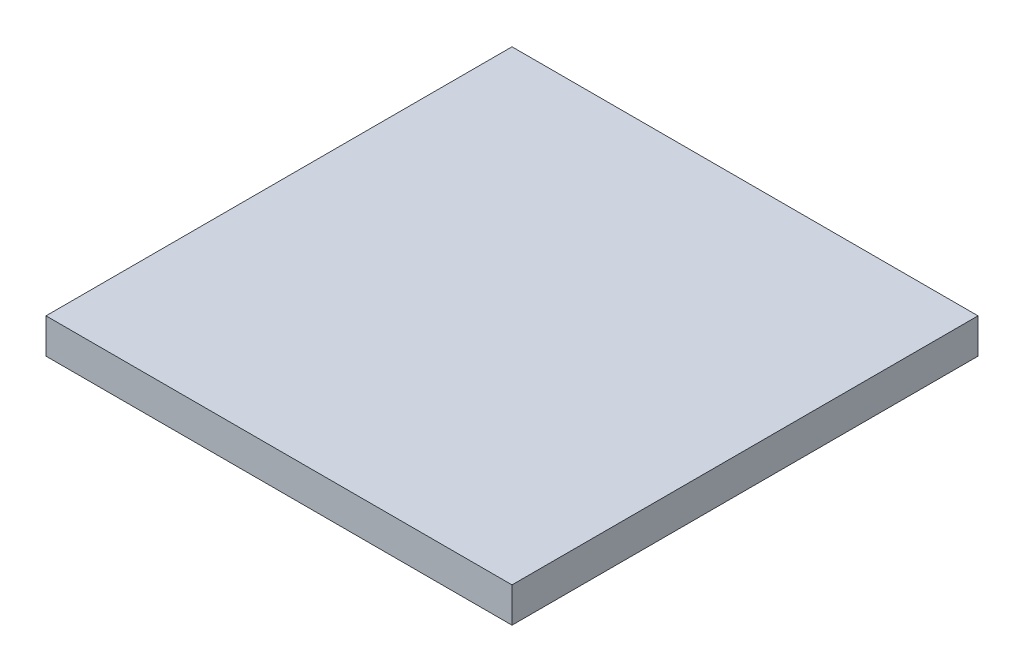
SolidWorks part; units mm, degrees
ref_plane "Alzado" through (0, 0, 0) normal (0, 0, 1) x (1, 0, 0)
ref_plane "Planta" through (0, 0, 0) normal (0, 1, 0) x (1, 0, 0)
ref_plane "Vista lateral" through (0, 0, 0) normal (1, 0, 0) x (0, 0, -1)
sketch "Croquis1" plane through (0, 0, 0) normal (0, 0, 1) x (1, 0, 0)
  line L1 (254, -19.05) -> (-254, -19.05)
  line L2 (254, -19.05) -> (254, 19.05)
  line L3 (254, 19.05) -> (-254, 19.05)
  line L4 (-254, -19.05) -> (-254, 19.05)
  line L5 (254, -19.05) -> (-254, 19.05) construction
  line L6 (254, 19.05) -> (-254, -19.05) construction
  point P0 (0, 0)
  dimension "D1" = 38.1
  dimension "D2" = 508
extrude "Saliente-Extruir1" add sketch "Croquis1" against normal blind 508
